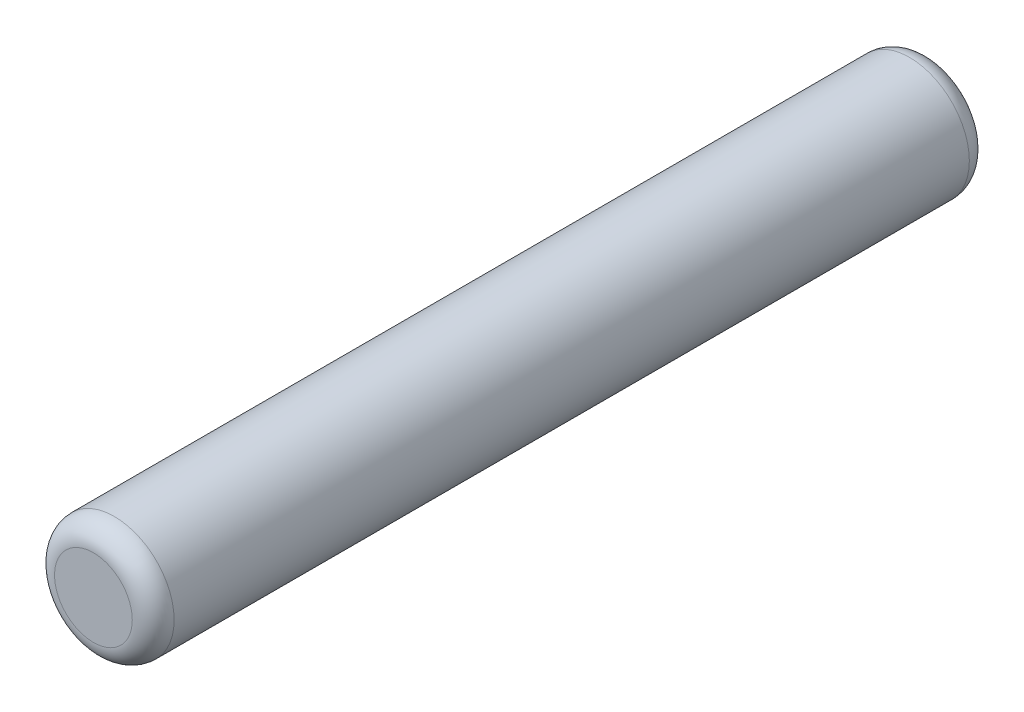
SolidWorks part; units mm, degrees
ref_plane "Front" through (0, 0, 0) normal (0, 0, 1) x (1, 0, 0)
ref_plane "Top" through (0, 0, 0) normal (0, 1, 0) x (1, 0, 0)
ref_plane "Right" through (0, 0, 0) normal (1, 0, 0) x (0, 0, -1)
sketch "Sketch1" plane through (0, 0, 0) normal (0, 0, 1) x (1, 0, 0)
  circle A0 centre (0, 0) radius 1
  dimension "D1" = 2
extrude "Boss-Extrude1" add sketch "Sketch1" along normal mid plane 14
fillet "Fillet1" radius 0.35 2 edges at (1, 0, -7) (1, 0, 7)
